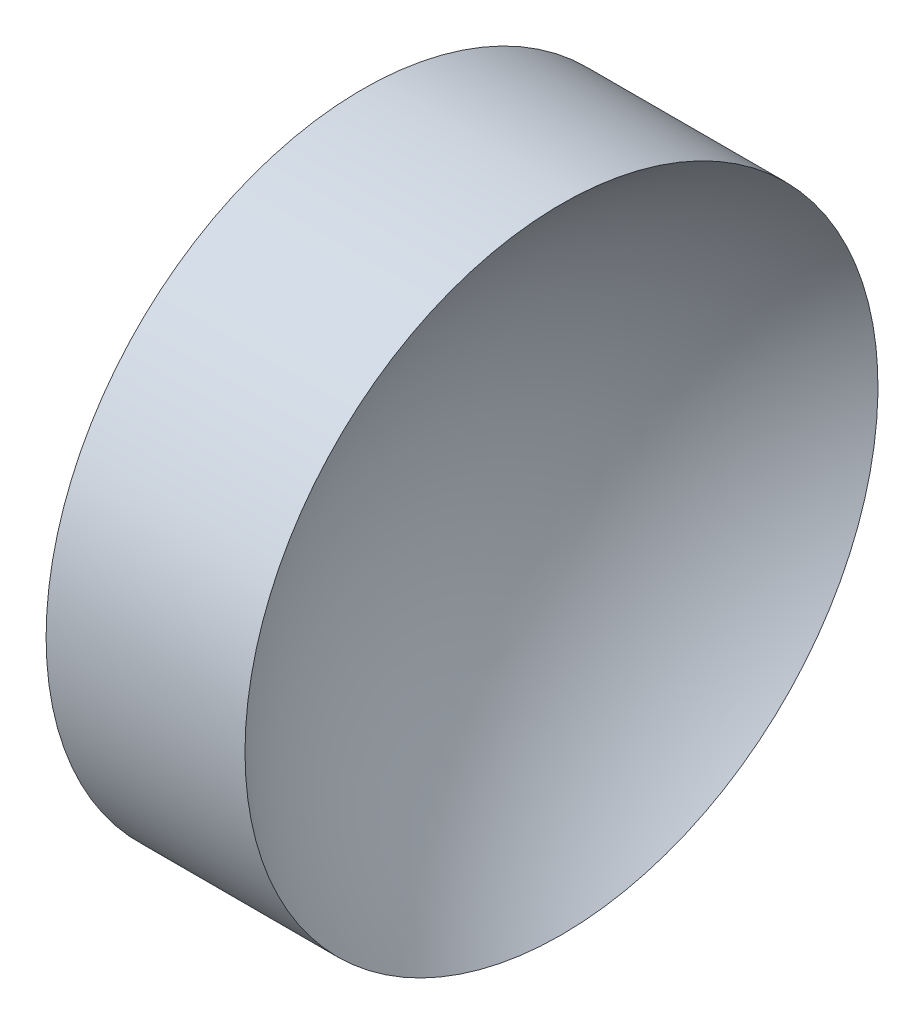
SolidWorks part; units mm, degrees
ref_plane "前视基准面" through (0, 0, 0) normal (0, 0, 1) x (1, 0, 0)
ref_plane "上视基准面" through (0, 0, 0) normal (0, 1, 0) x (1, 0, 0)
ref_plane "右视基准面" through (0, 0, 0) normal (1, 0, 0) x (0, 0, -1)
sketch "草图1" plane through (0, 0, 0) normal (0, 0, 1) x (1, 0, 0)
  line L0 (56.1009, 32.6108) -> (68.2773, 32.6108) construction
  line L1 (57.5323, 32.6108) -> (57.5323, 45.1108)
  line L2 (57.5323, 45.1108) -> (65.3878, 45.1108)
  line L3 (59.5323, 32.6108) -> (57.5323, 32.6108)
  arc A0 (65.3878, 45.1108) -> (59.5323, 32.6108) centre (75.8023, 32.6108) ccw
revolve "旋转1" add sketch "草图1" angle 360 about L0
